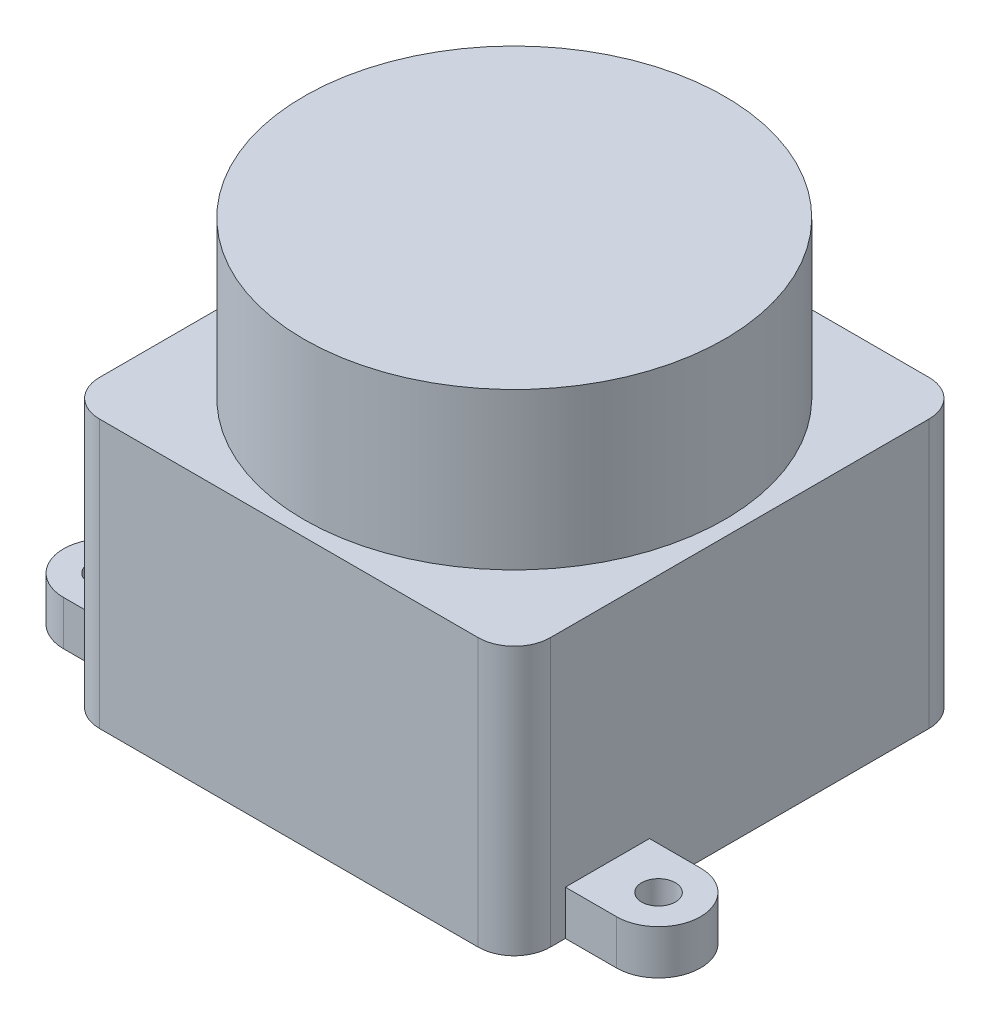
SolidWorks part; units mm, degrees
ref_plane "Plan de face" through (0, 0, 0) normal (0, 0, 1) x (1, 0, 0)
ref_plane "Plan de dessus" through (0, 0, 0) normal (0, 1, 0) x (1, 0, 0)
ref_plane "Plan de droite" through (0, 0, 0) normal (1, 0, 0) x (0, 0, -1)
sketch "Esquisse1" plane through (0, 0, 0) normal (0, 1, 0) x (1, 0, 0)
  line L1 (-18.75, -18.75) -> (18.75, -18.75)
  line L2 (-18.75, -18.75) -> (-18.75, 18.75)
  line L3 (-18.75, 18.75) -> (18.75, 18.75)
  line L4 (18.75, -18.75) -> (18.75, 18.75)
  line L5 (-18.75, -18.75) -> (18.75, 18.75) construction
  line L6 (-18.75, 18.75) -> (18.75, -18.75) construction
  point P0 (0, 0)
  dimension "D1" = 37.5
extrude "Boss.-Extru.1" add sketch "Esquisse1" along normal blind 22.3
fillet "Congé1" radius 3 4 edges at (18.75, 11.15, -18.75) (-18.75, 11.15, -18.75) (-18.75, 11.15, 18.75) (18.75, 11.15, 18.75)
sketch "Esquisse2" plane through (0, 22.3, 0) normal (0, 1, 0) x (1, 0, 0)
  circle A0 centre (0, 0) radius 17.5
  dimension "D1" = 35
extrude "Boss.-Extru.2" add sketch "Esquisse2" along normal blind 13
sketch "Esquisse3" plane through (0, 0, 0) normal (0, -1, 0) x (1, 0, 0)
  line L0 (-23, 11) -> (23, 11) construction
  line L1 (0, 11) -> (0, -21.7261) construction
  line L2 (-23, 14.5) -> (-18.75, 14.5)
  line L3 (-18.75, -15.75) -> (-18.75, 15.75) construction
  line L4 (-23, 7.5) -> (-18.75, 7.5)
  line L5 (23, 7.5) -> (18.75, 7.5)
  line L6 (18.75, 15.75) -> (18.75, -15.75) construction
  line L7 (23, 14.5) -> (18.75, 14.5)
  line L8 (-3.5, -21.7261) -> (-3.5, -18.75)
  line L9 (15.75, -18.75) -> (-15.75, -18.75) construction
  line L10 (3.5, -21.7261) -> (3.5, -18.75)
  line L11 (-18.75, 7.5) -> (-18.75, 14.5)
  line L12 (-3.5, -18.75) -> (3.5, -18.75)
  line L13 (18.75, 7.5) -> (18.75, 14.5)
  circle A0 centre (-23, 11) radius 1.4
  circle A1 centre (23, 11) radius 1.4
  circle A2 centre (0, -21.7261) radius 1.4
  circle A3 centre (-23, 11) radius 3.5
  circle A4 centre (23, 11) radius 3.5
  circle A5 centre (0, -21.7261) radius 3.5
  point P3 (0, 11)
  line M9 (-15.75, -18.75) -> (15.75, -18.75)
  line M11 (18.75, -15.75) -> (18.75, 15.75)
  line M15 (-18.75, 15.75) -> (-18.75, -15.75)
  dimension "D1" = 2.8
  dimension "D5" = 7
  dimension "D2" = 11
  dimension "D3" = 46
  dimension "D4" = 40
extrude "Boss.-Extru.3" add sketch "Esquisse3" against normal blind 3.7 contours A3 A0 | A3 L4 L2 M15 | A4 L7 L5 M11 | A5 L12 A2 | A5 L8 M9 | A5 L10 M9 | A1
